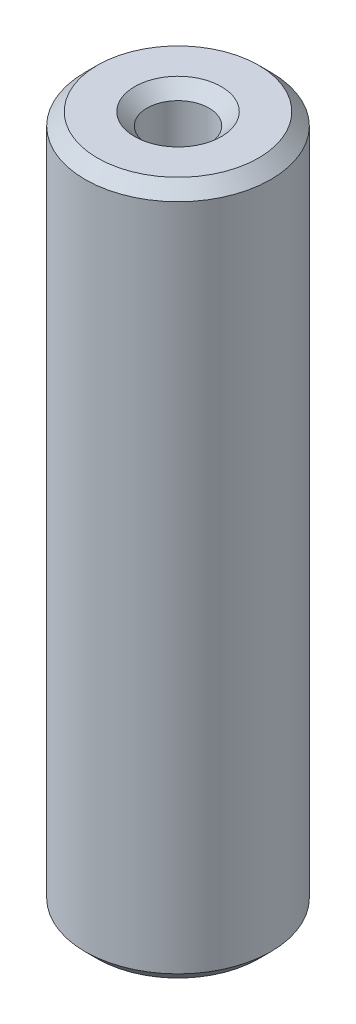
SolidWorks part; units mm, degrees
ref_plane "Plan de face" through (0, 0, 0) normal (0, 0, 1) x (1, 0, 0)
ref_plane "Plan de dessus" through (0, 0, 0) normal (0, 1, 0) x (1, 0, 0)
ref_plane "Plan de droite" through (0, 0, 0) normal (1, 0, 0) x (0, 0, -1)
sketch "Esquisse1" plane through (0, 0, 0) normal (0, 1, 0) x (1, 0, 0)
  circle A0 centre (0, 0) radius 7.5
  circle A1 centre (0, 0) radius 2.5
  dimension "D1" = 15
  dimension "D2" = 5
extrude "Extrusion1" add sketch "Esquisse1" along normal blind 56
chamfer "Chanfrein1" distance 1 angle 45 4 edges at (0, 0, 2.5) (0, 0, 7.5) (0, 56, 2.5) (0, 56, 7.5)
